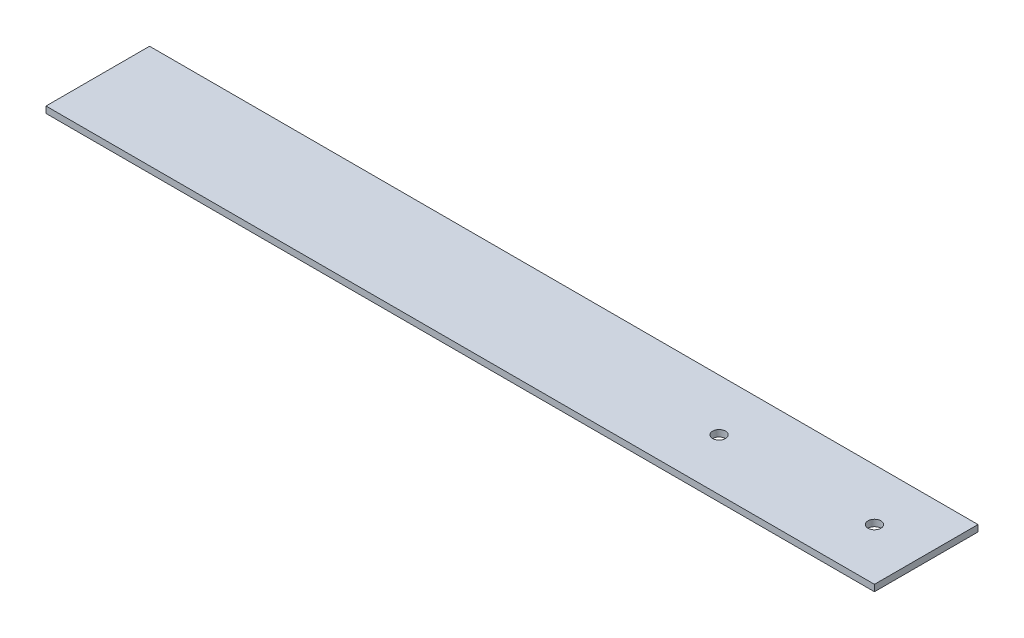
SolidWorks part; units mm, degrees
ref_plane "Front" through (0, 0, 0) normal (0, 0, 1) x (1, 0, 0)
ref_plane "Top" through (0, 0, 0) normal (0, 1, 0) x (1, 0, 0)
ref_plane "Right" through (0, 0, 0) normal (1, 0, 0) x (0, 0, -1)
sketch "Sketch1" plane through (0, 0, 0) normal (0, 1, 0) x (1, 0, 0)
  line L1 (0, 0) -> (406.4, 0)
  line L2 (0, 0) -> (0, 50.8)
  line L3 (0, 50.8) -> (406.4, 50.8)
  line L4 (406.4, 0) -> (406.4, 50.8)
  line L5 (0, 0) -> (406.4, 50.8) construction
  line L6 (0, 50.8) -> (406.4, 0) construction
  point P4 (203.2, 25.4)
  dimension "D1" = 50.8
  dimension "D2" = 406.4
extrude "Boss-Extrude1" add sketch "Sketch1" along normal blind 3.175
sketch "Sketch2" plane through (0, 3.175, 0) normal (0, 1, 0) x (1, 0, 0)
  line L0 (406.4, 0) -> (406.4, 50.8) construction
  circle A0 centre (381, 25.4) radius 3.175
  circle A1 centre (304.8, 25.4) radius 3.175
  dimension "D1" = 6.35
  dimension "D3" = 6.35
  dimension "D4" = 76.2
  dimension "D2" = 25.4
extrude "Cut-Extrude1" cut sketch "Sketch2" against normal through all
